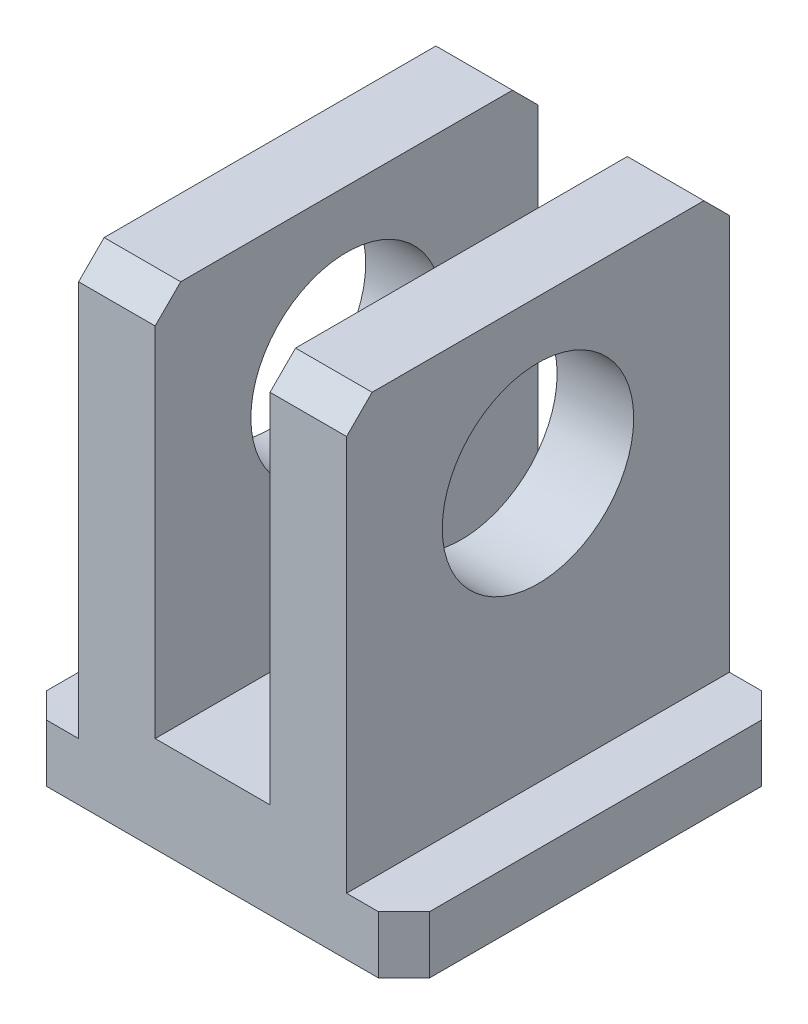
SolidWorks part; units mm, degrees
material "회주철"
ref_plane "정면" through (0, 0, 0) normal (0, 0, 1) x (1, 0, 0)
ref_plane "윗면" through (0, 0, 0) normal (0, 1, 0) x (1, 0, 0)
ref_plane "우측면" through (0, 0, 0) normal (1, 0, 0) x (0, 0, -1)
sketch "스케치1" plane through (0, 0, 0) normal (1, 0, 0) x (0, 0, -1)
  line L0 (0, 0) -> (30, 0)
  line L1 (30, 0) -> (30, 37.5)
  line L2 (30, 37.5) -> (0, 37.5)
  line L3 (0, 37.5) -> (0, 0)
  dimension "D1" = 30
  dimension "D2" = 37.5
extrude "보스-돌출1" add sketch "스케치1" along normal mid plane 30
chamfer "모따기1" distance 2 angle 45 2 edges at (0, 37.5, -30) (0, 37.5, 0)
sketch "스케치2" plane through (0, 0, 0) normal (0, 0, 1) x (1, 0, 0)
  line L0 (-15, 37.5) -> (-15, 4.5)
  line L3 (15, 37.5) -> (15, 4.5)
  line L4 (-15, 37.5) -> (15, 37.5) construction
  line L5 (-15, 37.5) -> (-10.5, 37.5)
  line L6 (-15, 4.5) -> (-10.5, 4.5)
  line L7 (-10.5, 37.5) -> (-10.5, 4.5)
  line L8 (10.5, 37.5) -> (10.5, 4.5)
  line L9 (-4.5, 7.5) -> (4.5, 7.5)
  line L10 (-4.5, 37.5) -> (-4.5, 7.5)
  line L11 (4.5, 37.5) -> (4.5, 7.5)
  line L12 (-4.5, 37.5) -> (4.5, 37.5)
  line L13 (-15, 37.5) -> (15, 37.5) construction
  line L14 (10.5, 37.5) -> (15, 37.5)
  line L16 (-15, 4.5) -> (15, 4.5) construction
  line L17 (10.5, 4.5) -> (15, 4.5)
  dimension "D1" = 33
  dimension "D2" = 10.5
  dimension "D3" = 10.5
  dimension "D4" = 6
  dimension "D5" = 4.5
  dimension "D6" = 4.5
  dimension "D7" = 7.5
extrude "컷-돌출1" cut sketch "스케치2" against normal up to next
sketch "스케치3" plane through (0, 0, 0) normal (1, 0, 0) x (0, 0, -1)
  circle A0 centre (15, 25.5) radius 7.5
  dimension "D1" = 15
  dimension "D2" = 25.5
  dimension "D3" = 15
extrude "컷-돌출2" cut sketch "스케치3" against normal mid plane 21
chamfer "모따기2" distance 2 angle 45 4 edges at (-15, 2.25, -30) (-15, 2.25, 0) (15, 2.25, -30) (15, 2.25, 0)
